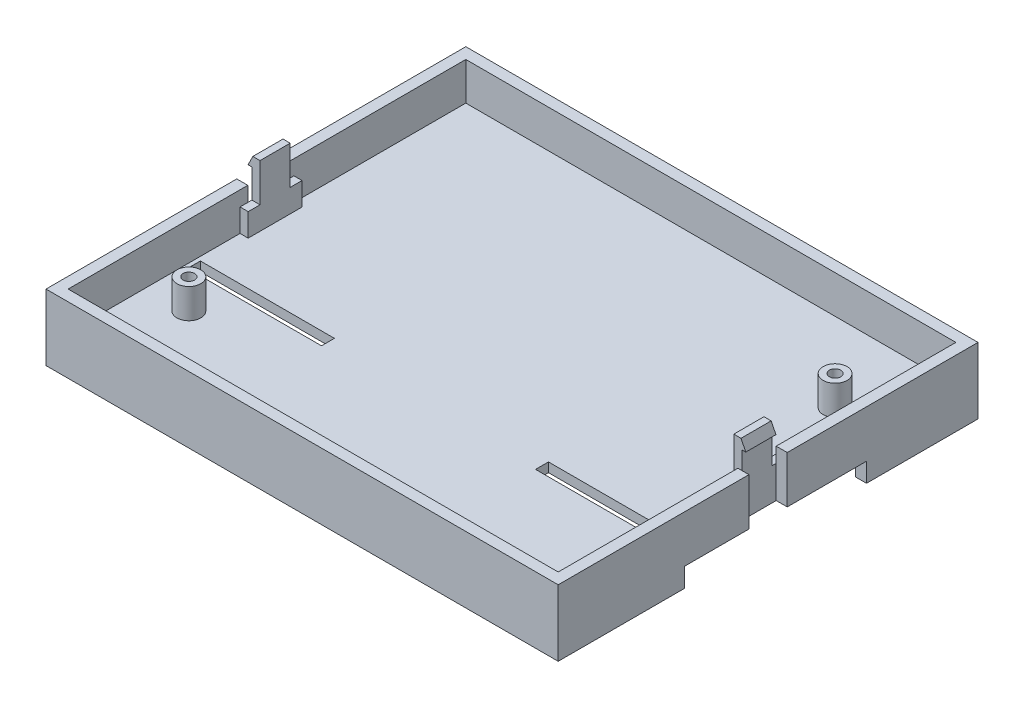
SolidWorks part; units mm, degrees
ref_plane "Alzado" through (0, 0, 0) normal (0, 0, 1) x (1, 0, 0)
ref_plane "Planta" through (0, 0, 0) normal (0, 1, 0) x (1, 0, 0)
ref_plane "Vista lateral" through (0, 0, 0) normal (1, 0, 0) x (0, 0, -1)
sketch "Sketch1" plane through (0, 0, 0) normal (0, 1, 0) x (1, 0, 0)
  line L1 (-53.5, -43.85) -> (53.5, -43.85)
  line L2 (-53.5, -43.85) -> (-53.5, 43.85)
  line L3 (-53.5, 43.85) -> (53.5, 43.85)
  line L4 (53.5, -43.85) -> (53.5, 43.85)
  line L5 (-53.5, -43.85) -> (53.5, 43.85) construction
  line L6 (-53.5, 43.85) -> (53.5, -43.85) construction
  point P0 (0, 0)
  dimension "D1" = 107
  dimension "D2" = 87.7
extrude "Boss-Extrude1" add sketch "Sketch1" along normal blind 13.85
sketch "Sketch2" plane through (0, 13.85, 0) normal (0, 1, 0) x (1, 0, 0)
  line L8 (51.19, -41.54) -> (51.19, 41.54)
  line L9 (51.19, 41.54) -> (-51.19, 41.54)
  line L10 (-51.19, 41.54) -> (-51.19, -41.54)
  line L11 (-51.19, -41.54) -> (51.19, -41.54)
  line L12 (51.19, -41.54) -> (51.19, 41.54)
  line L13 (51.19, 41.54) -> (-51.19, 41.54)
  line L14 (-51.19, 41.54) -> (-51.19, -41.54)
  line L15 (-51.19, -41.54) -> (51.19, -41.54)
  dimension "D1" = 2.31
extrude "Cut-Extrude1" cut sketch "Sketch2" against normal blind 7.9
sketch "Sketch3" plane through (0, 0, 0) normal (0, -1, 0) x (1, 0, 0)
  line L0 (-51.19, -41.54) -> (-51.19, 41.54) construction
  line L1 (-51.19, 41.54) -> (51.19, 41.54)
  line L2 (-51.19, 41.54) -> (-51.19, 19.24)
  line L3 (-51.19, 19.24) -> (-23.5, 19.24)
  line L4 (51.19, 41.54) -> (51.19, 19.24)
  line L5 (-51.19, 41.54) -> (51.19, 41.54) construction
  line L6 (51.19, 41.54) -> (51.19, -41.54) construction
  line L7 (-23.5, 19.24) -> (-23.5, 14.74)
  line L8 (-23.5, 14.74) -> (-49.4, 14.74)
  line L9 (-53.5, -43.85) -> (-53.5, 43.85) construction
  line L10 (-53.5, 17.44) -> (-53.5, -20.56)
  line L11 (-41.0677, -20.56) -> (-6.19, -20.56)
  line L12 (53.5, 43.85) -> (53.5, -43.85) construction
  line L13 (53.5, -20.56) -> (53.5, 17.44)
  line L14 (0, 0) -> (0, 18.4212) construction
  line L15 (23.5, 14.74) -> (23.5, 19.24)
  line L16 (23.5, 19.24) -> (51.19, 19.24)
  line L17 (-51.19, -41.54) -> (-10.19, -41.54)
  line L18 (51.19, -41.54) -> (51.19, -20.56)
  line L19 (-51.19, -41.54) -> (-51.19, -20.56)
  line L20 (-10.19, -41.54) -> (-10.19, -22.86)
  line L21 (10.19, -41.54) -> (10.19, -22.86)
  line L22 (6.19, -20.56) -> (6.19, -43.85)
  line L23 (-6.19, -43.85) -> (6.19, -43.85)
  line L24 (51.19, -20.56) -> (53.5, -20.56)
  line L25 (10.19, -41.54) -> (51.19, -41.54)
  line L26 (53.5, -43.85) -> (-53.5, -43.85) construction
  line L28 (51.19, -41.54) -> (-51.19, -41.54) construction
  line L29 (-10.19, -22.86) -> (-40.69, -22.86)
  line L30 (42.7044, -23.54) -> (40.69, -22.86)
  line L31 (-51.19, -20.56) -> (-53.5, -20.56)
  line L32 (-41.0677, -20.56) -> (-43.44, -21.3608)
  line L33 (-43.44, -21.3608) -> (-42.7044, -23.54)
  line L34 (-42.7044, -23.54) -> (-40.69, -22.86)
  line L35 (43.44, -21.3608) -> (42.7044, -23.54)
  line L36 (41.0677, -20.56) -> (43.44, -21.3608)
  line L37 (10.19, -22.86) -> (40.69, -22.86)
  line L38 (41.0677, -20.56) -> (6.19, -20.56)
  line L39 (-49.4, 17.44) -> (-53.5, 17.44)
  line L40 (-49.4, 17.44) -> (-49.4, 14.74)
  line L41 (49.4, 17.44) -> (53.5, 17.44)
  line L42 (49.4, 17.44) -> (49.4, 14.74)
  line L43 (23.5, 14.74) -> (49.4, 14.74)
  line L44 (-6.19, -20.56) -> (-6.19, -43.85)
  dimension "D1" = 22.3
  dimension "D2" = 30
  dimension "D3" = 4.5
  dimension "D4" = 4
  dimension "D5" = 4
  dimension "D6" = 41
  dimension "D7" = 2.3
  dimension "D8" = 7.75
  dimension "D9" = 2.3
  dimension "D10" = 35.3
  dimension "D11" = 18
  dimension "D12" = 30.5
  dimension "D13" = 30.5
  dimension "D14" = 25.9
  dimension "D15" = 1.8
extrude "Cut-Extrude2" cut sketch "Sketch3" against normal blind 4
sketch "Sketch4" plane through (0, 5.95, 0) normal (0, 1, 0) x (1, 0, 0)
  circle A0 centre (42.5, 25) radius 1.2
  circle A1 centre (-42.5, -25) radius 1.2
  circle A2 centre (-42.5, -25) radius 2.5
  circle A3 centre (42.5, 25) radius 2.5
  dimension "D1" = 2.4
  dimension "D6" = 5
  dimension "D2" = 25
  dimension "D3" = 25
  dimension "D4" = 42.5
  dimension "D5" = 42.5
extrude "Boss-Extrude2" add sketch "Sketch4" along normal blind 6.2
sketch "Sketch5" plane through (0, 5.95, 0) normal (0, 1, 0) x (1, 0, 0)
  line L0 (-49.4, -17.44) -> (-53.5, -17.44) construction
  line L1 (-50.36, -17.44) -> (-22.36, -17.44)
  line L2 (-50.36, -17.44) -> (-50.36, -14.74)
  line L3 (-50.36, -14.74) -> (-22.36, -14.74)
  line L4 (-22.36, -17.44) -> (-22.36, -14.74)
  line L5 (-23.5, -14.74) -> (-49.4, -14.74) construction
  line L6 (-53.5, 43.85) -> (-53.5, -43.85) construction
  line L7 (0, 0) -> (0, -23.0009) construction
  line L8 (22.36, -17.44) -> (22.36, -14.74)
  line L9 (50.36, -14.74) -> (22.36, -14.74)
  line L10 (50.36, -17.44) -> (50.36, -14.74)
  line L11 (50.36, -17.44) -> (22.36, -17.44)
  dimension "D1" = 3.14
  dimension "D2" = 28
extrude "Cut-Extrude3" cut sketch "Sketch5" against normal blind 3.5
chamfer "Chamfer1" distance 2 angle 45 2 edges at (-36.45, 2.45, 14.74) (36.45, 2.45, 14.74)
sketch "Sketch6" plane through (-53.5, 0, 0) normal (-1, 0, 0) x (0, 0, 1)
  line L0 (-43.85, 13.85) -> (43.85, 13.85) construction
  line L1 (-4, 13.85) -> (4, 13.85)
  line L2 (-4, 13.85) -> (-4, 4)
  line L3 (-4, 4) -> (4, 4)
  line L4 (4, 13.85) -> (4, 4)
  line L5 (17.44, 4) -> (-20.56, 4) construction
  point P8 (0, 4)
  dimension "D1" = 8
extrude "Cut-Extrude4" cut sketch "Sketch6" against normal blind 2.31
sketch "Sketch7" plane through (-51.19, 0, 0) normal (1, 0, 0) x (0, 0, -1)
  line L0 (-4, 5.95) -> (-41.54, 5.95) construction
  line L1 (-5.625, 5.95) -> (5.625, 5.95)
  line L2 (-5.625, 5.95) -> (-5.625, 10.75)
  line L3 (-5.625, 10.75) -> (5.625, 10.75)
  line L4 (5.625, 5.95) -> (5.625, 10.75)
  point P6 (0, 5.95)
  dimension "D1" = 11.25
  dimension "D2" = 4.8
extrude "Boss-Extrude3" add sketch "Sketch7" along normal blind 1.7
sketch "Sketch8" plane through (0, 0, 0) normal (0, 0, 1) x (1, 0, 0)
  line L0 (-49.49, 10.75) -> (-49.49, 18.75)
  line L1 (-49.49, 18.75) -> (-50.99, 18.75)
  line L2 (-50.99, 18.75) -> (-51.99, 16.75)
  line L3 (-51.99, 16.75) -> (-51.19, 16.75)
  line L4 (-51.19, 16.75) -> (-51.19, 10.75)
  line L5 (-51.19, 10.75) -> (-49.49, 10.75)
  line L6 (51.19, 5.95) -> (-51.19, 5.95) construction
  dimension "D1" = 12.8
  dimension "D2" = 2.5
  dimension "D3" = 2
  dimension "D4" = 1.5
extrude "Boss-Extrude4" add sketch "Sketch8" along normal mid plane 6.3
mirror "Mirror1" about plane through (0, 0, 0) normal (1, 0, 0) of "Boss-Extrude4", "Boss-Extrude3", "Cut-Extrude4"
